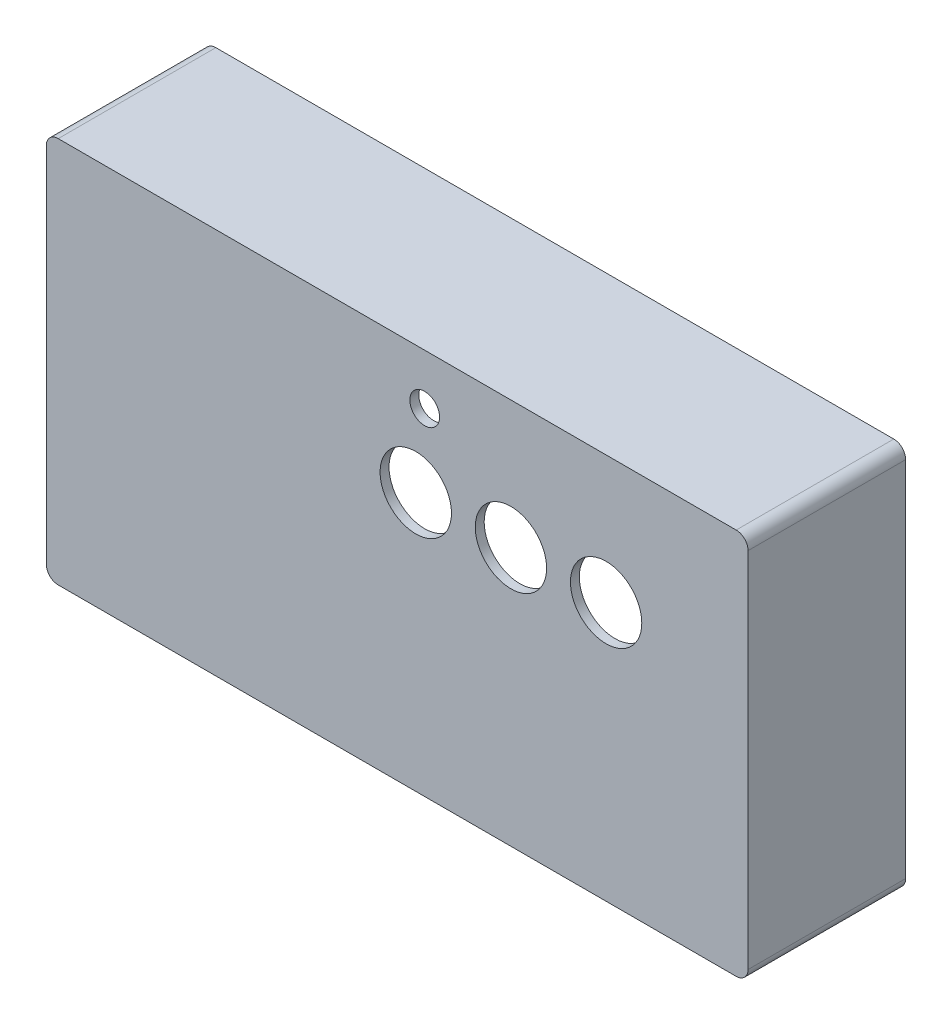
SolidWorks part; units mm, degrees
ref_plane "Front" through (0, 0, 0) normal (0, 0, 1) x (1, 0, 0)
ref_plane "Top" through (0, 0, 0) normal (0, 1, 0) x (1, 0, 0)
ref_plane "Right" through (0, 0, 0) normal (1, 0, 0) x (0, 0, -1)
sketch "Sketch1" plane through (0, 0, 0) normal (0, 0, 1) x (1, 0, 0)
  line L1 (-56.125, 30) -> (56.125, 30)
  line L2 (-56.125, 30) -> (-56.125, -30)
  line L3 (-56.125, -30) -> (56.125, -30)
  line L4 (56.125, 30) -> (56.125, -30)
  line L5 (-56.125, 30) -> (56.125, -30) construction
  line L6 (-56.125, -30) -> (56.125, 30) construction
  point P0 (0, 0)
  dimension "D1" = 112.25
  dimension "D2" = 60
sketch "Sketch2" plane through (0, 0, 0) normal (0, 0, 1) x (1, 0, 0)
  line L0 (-59, 32.5) -> (-59, -32.5)
  line L1 (-57, 30.5) -> (57, 30.5) construction
  line L2 (-57, 30.5) -> (-57, -30.5) construction
  line L3 (-57, -30.5) -> (57, -30.5) construction
  line L4 (57, 30.5) -> (57, -30.5) construction
  line L5 (-57, 30.5) -> (57, -30.5) construction
  line L6 (-57, -30.5) -> (57, 30.5) construction
  line L7 (-59, -32.5) -> (59, -32.5)
  line L8 (59, 32.5) -> (59, -32.5)
  line L9 (-59, 32.5) -> (59, 32.5)
  point P0 (0, 0)
  dimension "D1" = 61
  dimension "D2" = 114
  dimension "D3" = 2
extrude "Boss-Extrude2" add sketch "Sketch2" along normal blind 1.5
sketch "Sketch4" plane through (0, 0, 0) normal (0, 0, 1) x (1, 0, 0)
  line L0 (57, -30.5) -> (57, 30.5)
  line L1 (-59, -32.5) -> (59, -32.5)
  line L2 (-59, -32.5) -> (-59, 32.5)
  line L3 (-59, 32.5) -> (59, 32.5)
  line L4 (59, -32.5) -> (59, 32.5)
  line L5 (-57, 30.5) -> (57, 30.5)
  line L6 (-57, -30.5) -> (-57, 30.5)
  line L7 (-57, -30.5) -> (57, -30.5)
  dimension "D1" = 2
extrude "Boss-Extrude3" add sketch "Sketch4" against normal blind 25
fillet "Fillet2" radius 2 4 edges at (-59, 32.5, -11.75) (-59, -32.5, -11.75) (59, 32.5, -11.75) (59, -32.5, -11.75)
fillet "Fillet3" radius 1 4 edges at (-57, -30.5, -12.5) (-57, 30.5, -12.5) (57, 30.5, -12.5) (57, -30.5, -12.5)
sketch "Sketch5" plane through (0, 0, 1.5) normal (0, 0, 1) x (1, 0, 0)
  line L1 (-56.125, 30) -> (56.125, 30) construction
  line L2 (56.125, 30) -> (56.125, -30) construction
  line L3 (35.125, 11) -> (19.125, 11) construction
  line L4 (19.125, 11) -> (3.125, 11) construction
  circle A0 centre (35.125, 11) radius 6
  circle A1 centre (19.125, 11) radius 6
  circle A2 centre (3.125, 11) radius 6
  circle A3 centre (4.625, 24) radius 2.5
  dimension "D3" = 12
  dimension "D8" = 5
  dimension "D1" = 21
  dimension "D2" = 19
  dimension "D5" = 16
  dimension "D6" = 6
  dimension "D7" = 51.5
  dimension "D4" = 3
extrude "Cut-Extrude1" cut sketch "Sketch5" against normal through all
sketch "Sketch6" plane through (0, 0, 0) normal (0, 0, -1) x (-1, 0, 0)
  line L0 (-57, 30.5) -> (-57, 23)
  line L1 (56.125, 30) -> (-56.125, 30) construction
  line L2 (-57, 30.5) -> (-49.125, 30.5)
  line L3 (-49.125, 30.5) -> (-49.125, 26)
  line L4 (-56.125, 30) -> (-56.125, -30) construction
  line L5 (-57, 23) -> (-52.125, 23)
  line L6 (32.875, 30.5) -> (38.875, 30.5)
  line L7 (38.875, 30.5) -> (38.875, 26)
  line L8 (32.875, 30.5) -> (32.875, 26)
  line L9 (-52.125, 26) -> (35.875, 26) construction
  line L10 (-3.125, 11) -> (-3.125, 30) construction
  line L11 (-56, 30.5) -> (56, 30.5) construction
  line L12 (-6.625, 27.5) -> (0.375, 27.5)
  line L13 (-6.625, 27.5) -> (-6.625, 30.5)
  line L14 (-6.625, 30.5) -> (0.375, 30.5)
  line L15 (0.375, 27.5) -> (0.375, 30.5)
  line L16 (-6.625, 27.5) -> (0.375, 30.5) construction
  line L17 (-6.625, 30.5) -> (0.375, 27.5) construction
  line L18 (-57, -29.5) -> (-57, 29.5) construction
  line L19 (-56, 30.5) -> (56, 30.5) construction
  circle A0 centre (-52.125, 26) radius 1
  arc A1 (-52.125, 23) -> (-49.125, 26) centre (-52.125, 26) ccw
  circle A2 centre (35.875, 26) radius 1
  arc A3 (32.875, 26) -> (38.875, 26) centre (35.875, 26) ccw
  point P21 (-3.125, 29)
  dimension "D1" = 2
  dimension "D2" = 3
  dimension "D3" = 4
  dimension "D4" = 4
  dimension "D5" = 92
  dimension "D6" = 2.5
  dimension "D7" = 7
extrude "Boss-Extrude4" add sketch "Sketch6" along normal blind 8
mirror "Mirror1" about plane through (0, 0, 0) normal (0, 1, 0) of "Boss-Extrude4"
fillet "Fillet4" radius 2 12 edges at (-38.875, 30.5, -4) (-32.875, 30.5, -4) (-0.375, 30.5, -4) (6.625, 30.5, -4) (57, 23, -4) (49.125, 30.5, -4) (-38.875, -30.5, -4) (-32.875, -30.5, -4) (6.625, -30.5, -4) (-0.375, -30.5, -4) (49.125, -30.5, -4) (57, -23, -4)
fillet "Fillet6" radius 2 4 edges at (-0.375, 27.5, -4) (6.625, 27.5, -4) (6.625, -27.5, -4) (-0.375, -27.5, -4)
